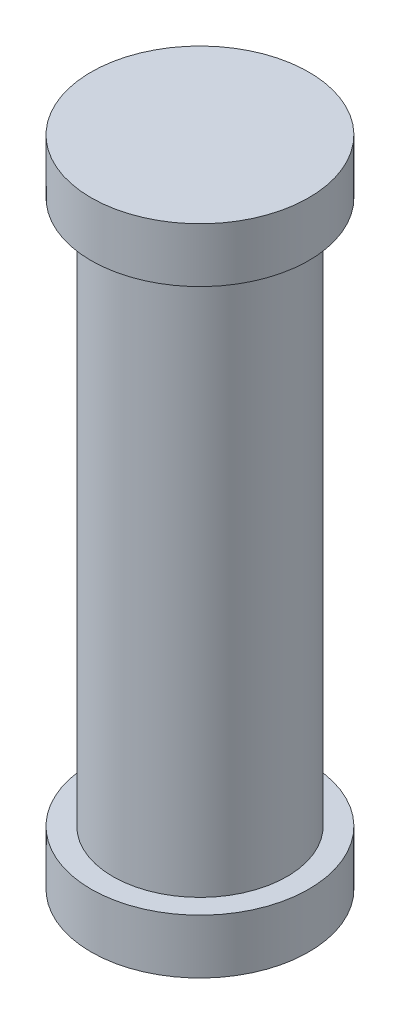
SolidWorks part; units mm, degrees
ref_plane "Front Plane" through (0, 0, 0) normal (0, 0, 1) x (1, 0, 0)
ref_plane "Top Plane" through (0, 0, 0) normal (0, 1, 0) x (1, 0, 0)
ref_plane "Right Plane" through (0, 0, 0) normal (1, 0, 0) x (0, 0, -1)
sketch "Sketch1" plane through (0, 0, 0) normal (0, 1, 0) x (1, 0, 0)
  circle A0 centre (0, 0) radius 2
extrude "Boss-Extrude1" add sketch "Sketch1" along normal blind 1
sketch "Sketch2" plane through (0, 1, 0) normal (0, 1, 0) x (1, 0, 0)
  circle A0 centre (0, 0) radius 1.6
extrude "Boss-Extrude2" add sketch "Sketch2" along normal blind 10
sketch "Sketch3" plane through (0, 11, 0) normal (0, 1, 0) x (1, 0, 0)
  circle A0 centre (0, 0) radius 2
extrude "Boss-Extrude3" add sketch "Sketch3" along normal blind 1
